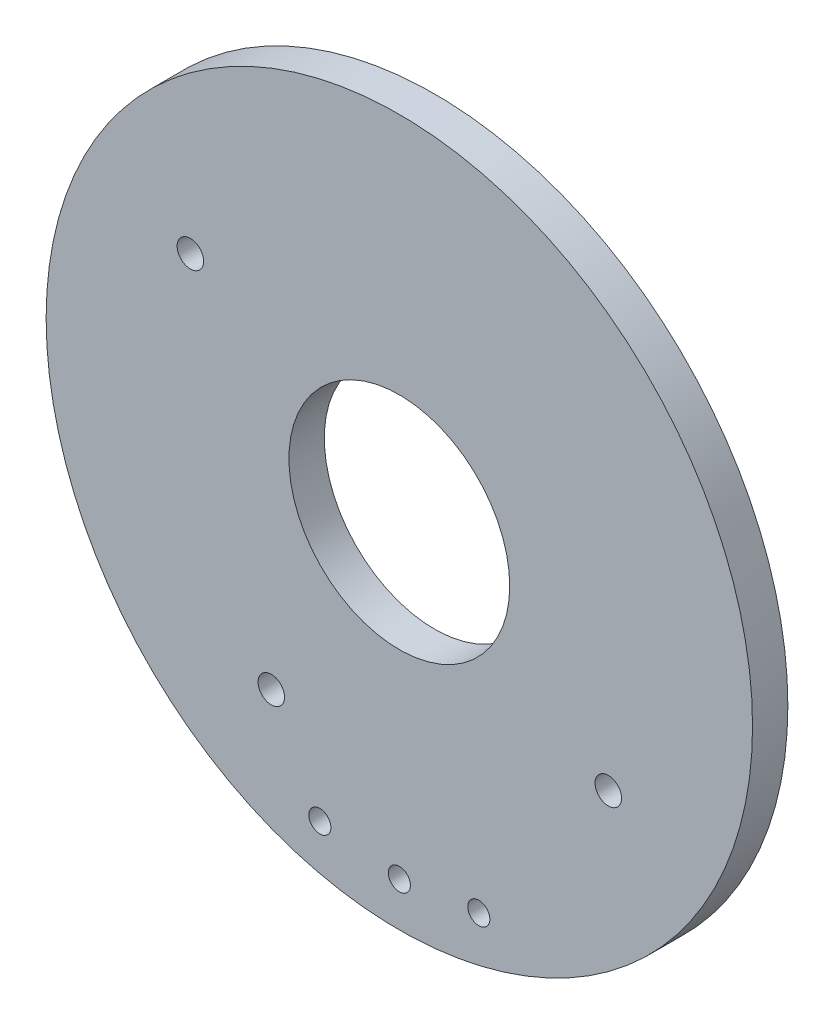
SolidWorks part; units mm, degrees
material "Fibra de vidrio-S"
ref_plane "Alzado" through (0, 0, 0) normal (0, 0, 1) x (1, 0, 0)
ref_plane "Planta" through (0, 0, 0) normal (0, 1, 0) x (1, 0, 0)
ref_plane "Vista lateral" through (0, 0, 0) normal (1, 0, 0) x (0, 0, -1)
sketch "Croquis1" plane through (0, 0, 0) normal (0, 0, 1) x (1, 0, 0)
  circle A0 centre (0, 0) radius 8
  circle A1 centre (0, 0) radius 2.5
  dimension "D1" = 5
  dimension "D2" = 16
extrude "Saliente-Extruir1" add sketch "Croquis1" along normal blind 0.8
sketch "Croquis2" plane through (0, 0, 0.8) normal (0, 0, 1) x (1, 0, 0)
  line L0 (0, -7) -> (0, 0) construction
  line L1 (0, 0) -> (-1.8, -6.7646) construction
  line L2 (-1.8, -6.7646) -> (0, -7) construction
  line L3 (0, 0) -> (1.8, -6.7646) construction
  line L4 (1.8, -6.7646) -> (0, -7) construction
  circle A0 centre (0, -7) radius 0.25
  circle A1 centre (-1.8, -6.7646) radius 0.25
  circle A2 centre (1.8, -6.7646) radius 0.25
  circle A3 centre (4.733, -2.9) radius 0.3
  circle A5 centre (-2.9, -4.733) radius 0.3
  circle A6 centre (-4.733, 2.9) radius 0.3
  circle A7 centre (2.9, 4.733) radius 0.3 [skipped]
  circle A9 centre (0, 0) radius 8 construction
  point P21 (0, 0)
  dimension "D1" = 0.5
  dimension "D4" = 0.6
  dimension "D2" = 7
  dimension "D3" = 3.6
  dimension "D6" = 2.9
  dimension "D7" = 4.733
  dimension "D5" = 4
extrude "Cortar-Extruir1" cut sketch "Croquis2" against normal blind 1.6
